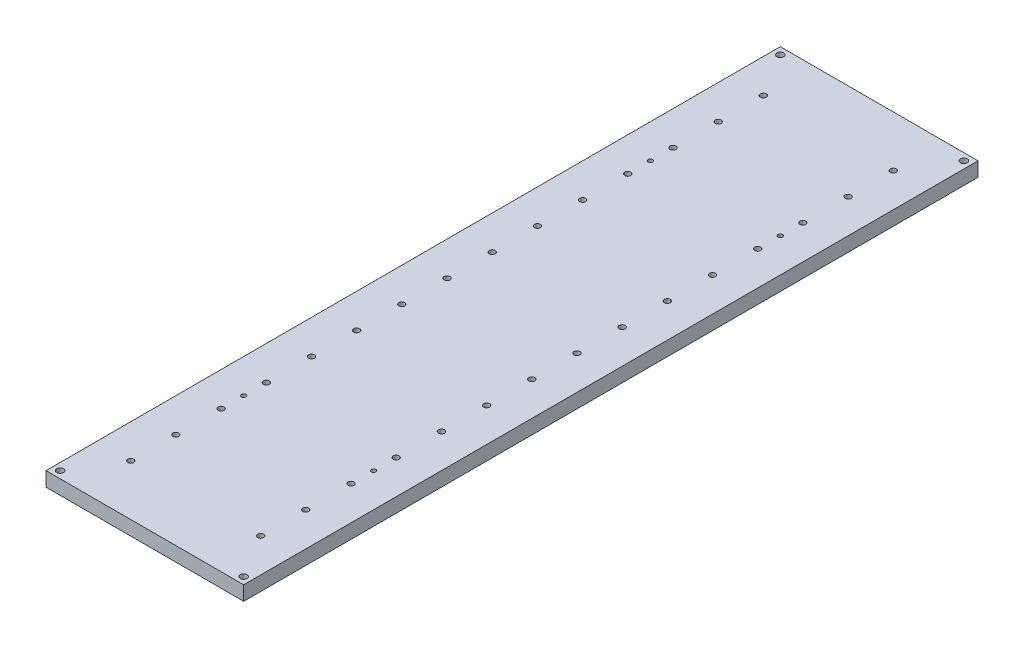
SolidWorks part; units mm, degrees
material "AISI 1020"
ref_plane "Plano frontal" through (0, 0, 0) normal (0, 0, 1) x (1, 0, 0)
ref_plane "Plano superior" through (0, 0, 0) normal (0, 1, 0) x (1, 0, 0)
ref_plane "Plano direito" through (0, 0, 0) normal (1, 0, 0) x (0, 0, -1)
sketch "Esboço1" plane through (0, 0, 0) normal (0, 0, 1) x (1, 0, 0)
  line L1 (-132, -12.7) -> (132, -12.7)
  line L2 (-132, -12.7) -> (-132, 12.7)
  line L3 (-132, 12.7) -> (132, 12.7)
  line L4 (132, -12.7) -> (132, 12.7)
  line L5 (-132, -12.7) -> (132, 12.7) construction
  line L6 (-132, 12.7) -> (132, -12.7) construction
  point P0 (0, 0)
  dimension "D1" = 25.4
  dimension "D2" = 264
extrude "Ressalto-extrusão1" add sketch "Esboço1" along normal mid plane 1180
sketch "Esboço3" plane through (132, 0, 0) normal (1, 0, 0) x (0, 0, -1)
  line L4 (-590, -12.7) -> (590, -12.7)
  line L5 (-590, 12.7) -> (-590, -12.7)
  line L6 (590, 12.7) -> (-590, 12.7)
  line L7 (590, -12.7) -> (590, 12.7)
  line L8 (-590, -12.7) -> (590, -12.7)
  line L9 (-590, 12.7) -> (-590, -12.7)
  line L10 (590, 12.7) -> (-590, 12.7)
  line L11 (590, -12.7) -> (590, 12.7)
  dimension "D1" = 0
sketch "Esboço4" plane through (-132, 0, 0) normal (-1, 0, 0) x (0, 0, 1)
  line L4 (-590, -12.7) -> (590, -12.7)
  line L5 (590, -12.7) -> (590, 12.7)
  line L6 (590, 12.7) -> (-590, 12.7)
  line L7 (-590, 12.7) -> (-590, -12.7)
  line L8 (-590, -12.7) -> (590, -12.7)
  line L9 (590, -12.7) -> (590, 12.7)
  line L10 (590, 12.7) -> (-590, 12.7)
  line L11 (-590, 12.7) -> (-590, -12.7)
  dimension "D1" = 0
extrude "Ressalto-extrusão3" add sketch "Esboço4" along normal blind 43
extrude "Ressalto-extrusão4" add sketch "Esboço3" along normal blind 43
hole_wizard "Rebaixo para parafuso Allen sextavado de M101" positions "Esboço6" profile "Esboço5" counterbore size "M10" standard "ISO" end condition through all
sketch "Esboço6" plane through (0, -12.7, 0) normal (0, -1, 0) x (-1, 0, 0)
  line L21 (175, 590) -> (175, -590) construction
  line L22 (-175, -590) -> (-175, 590) construction
  line L23 (-175, 590) -> (-175, -590) construction
  line L24 (175, -590) -> (175, 590) construction
  line L38 (-175, 590) -> (175, 590) construction
  point P4 (115, -320)
  point P10 (115, -240)
  point P84 (-115, 400)
  point P85 (-115, 240)
  point P86 (-115, 80)
  point P89 (-115, -80)
  point P90 (-115, -240)
  point P91 (-115, -400)
  point P154 (115, -480)
  point P155 (-115, -320)
  point P181 (-115, -160)
  point P186 (-115, 0)
  point P188 (-115, 160)
  point P196 (-115, 320)
  point P201 (-115, 480)
  point P202 (-115, 560)
  point P205 (115, 560)
  point P207 (-115, -480)
  point P210 (115, -400)
  point P215 (115, -80)
  point P217 (115, 0)
  point P219 (115, 80)
  point P221 (115, 160)
  point P223 (115, 320)
  point P225 (115, 240)
  point P227 (115, 400)
  point P229 (115, 480)
  point P234 (115, -160)
  point P240 (115, -560)
  point P244 (-115, -560)
  dimension "D2" = 60
  dimension "D3" = 80
  dimension "D5" = 80
  dimension "D6" = 80
  dimension "D7" = 80
  dimension "D8" = 80
  dimension "D9" = 80
  dimension "D10" = 80
  dimension "D11" = 60
  dimension "D12" = 60
  dimension "D13" = 60
  dimension "D14" = 60
  dimension "D15" = 60
  dimension "D16" = 60
  dimension "D17" = 60
  dimension "D18" = 80
  dimension "D19" = 80
  dimension "D20" = 80
  dimension "D21" = 80
  dimension "D22" = 80
  dimension "D23" = 80
  dimension "D24" = 80
  dimension "D25" = 80
  dimension "D26" = 80
  dimension "D27" = 80
  dimension "D28" = 80
  dimension "D29" = 30
  dimension "D30" = 80
  dimension "D31" = 80
  dimension "D32" = 80
  dimension "D33" = 80
  dimension "D34" = 80
  dimension "D35" = 80
  dimension "D36" = 80
  dimension "D37" = 80
  dimension "D38" = 80
  dimension "D39" = 80
  dimension "D40" = 80
  dimension "D41" = 30
  dimension "D42" = 60
  dimension "D43" = 60
  dimension "D44" = 60
  dimension "D45" = 60
  dimension "D46" = 60
  dimension "D47" = 60
  dimension "D48" = 60
  dimension "D49" = 60
  dimension "D50" = 60
  dimension "D51" = 60
  dimension "D52" = 60
  dimension "D53" = 60
  dimension "D54" = 60
  dimension "D55" = 60
  dimension "D56" = 60
  dimension "D57" = 60
sketch "Esboço5" plane through (-115, -12.7, 320) normal (1, 0, 0) x (0, 0, -1)
  line L0 (0, 0) -> (0, 25.4)
  line L1 (0, 25.4) -> (5.25, 25.4)
  line L3 (5.25, 25.4) -> (5.25, 10.6)
  line L4 (5.25, 10.6) -> (9, 10.6)
  line L5 (9, 10.6) -> (9, 0)
  line L7 (9, 0) -> (0, 0)
  line L11 (0, -6.35) -> (0, 107.95) construction
  dimension "Thru Hole Dia." = 10.5
  dimension "Thru Hole Depth" = 25.4
  dimension "C'Bore Dia." = 18
  dimension "C'Bore Depth" = 10.6
sketch "Esboço7" plane through (0, -12.7, 0) normal (0, -1, 0) x (1, 0, 0)
  line L0 (-175, 590) -> (-175, -590) construction
  line L1 (175, -590) -> (175, 590) construction
  circle A0 centre (-115, 360) radius 4
  circle A3 centre (115, 400) radius 5.25 construction
  circle A4 centre (115, 360) radius 4
  circle A5 centre (-115, 320) radius 5.25 construction
  point P6 (-88.8916, 480)
  point P7 (-88.8916, 480)
  dimension "D1" = 8
  dimension "D3" = 8
  dimension "D7" = 60
  dimension "D8" = 60
  dimension "D2" = 0
  dimension "D4" = 0
  dimension "D5" = 40
  dimension "D6" = 40
extrude "Corte-extrusão1" cut sketch "Esboço7" against normal through all
sketch "Esboço8" plane through (0, -12.7, 0) normal (0, -1, 0) x (1, 0, 0)
  line L0 (0, 652.0832) -> (0, 445.3456) construction
pattern_linear "Padrão linear1" count 2 spacing 720 along (0, 0, -1) of "Corte-extrusão1"
sketch "Esboço9" plane through (0, 0, 590) normal (0, 0, 1) x (1, 0, 0)
  line L4 (-175, -12.7) -> (175, -12.7)
  line L5 (175, -12.7) -> (175, 12.7)
  line L6 (175, 12.7) -> (-175, 12.7)
  line L7 (-175, 12.7) -> (-175, -12.7)
  line L8 (-175, -12.7) -> (175, -12.7)
  line L9 (175, -12.7) -> (175, 12.7)
  line L10 (175, 12.7) -> (-175, 12.7)
  line L11 (-175, 12.7) -> (-175, -12.7)
  dimension "D1" = 0
extrude "Ressalto-extrusão5" add sketch "Esboço9" along normal blind 60
sketch "Esboço10" plane through (0, 0, -590) normal (0, 0, -1) x (-1, 0, 0)
  line L4 (175, 12.7) -> (-175, 12.7)
  line L5 (-175, 12.7) -> (-175, -12.7)
  line L6 (-175, -12.7) -> (175, -12.7)
  line L7 (175, -12.7) -> (175, 12.7)
  line L8 (175, 12.7) -> (-175, 12.7)
  line L9 (-175, 12.7) -> (-175, -12.7)
  line L10 (-175, -12.7) -> (175, -12.7)
  line L11 (175, -12.7) -> (175, 12.7)
  dimension "D1" = 0
extrude "Ressalto-extrusão6" add sketch "Esboço10" along normal blind 60
sketch "Esboço12" plane through (0, 0, 650) normal (0, 0, 1) x (1, 0, 0)
  line L1 (-175, -12.7) -> (175, -12.7)
  line L2 (-175, -12.7) -> (-175, 12.7)
  line L3 (-175, 12.7) -> (175, 12.7)
  line L4 (175, -12.7) -> (175, 12.7)
  line L5 (-175, -12.7) -> (175, 12.7) construction
  line L6 (-175, 12.7) -> (175, -12.7) construction
  point P0 (0, 0)
extrude "Ressalto-extrusão7" [suppressed] add sketch "Esboço12" along normal blind 50
sketch "Esboço13" plane through (0, 0, -650) normal (0, 0, -1) x (-1, 0, 0)
  line L1 (175, -12.7) -> (-175, -12.7)
  line L2 (175, -12.7) -> (175, 12.7)
  line L3 (175, 12.7) -> (-175, 12.7)
  line L4 (-175, -12.7) -> (-175, 12.7)
  line L5 (175, -12.7) -> (-175, 12.7) construction
  line L6 (175, 12.7) -> (-175, -12.7) construction
  point P0 (0, 0)
extrude "Ressalto-extrusão8" [suppressed] add sketch "Esboço13" along normal blind 50
sketch "Esboço14" plane through (0, 0, 650) normal (0, 0, 1) x (1, 0, 0)
  line L1 (-175, -12.7) -> (175, -12.7)
  line L2 (-175, -12.7) -> (-175, 12.7)
  line L3 (-175, 12.7) -> (175, 12.7)
  line L4 (175, -12.7) -> (175, 12.7)
  line L5 (-175, -12.7) -> (175, 12.7) construction
  line L6 (-175, 12.7) -> (175, -12.7) construction
  point P0 (0, 0)
extrude "Ressalto-extrusão9" [suppressed] add sketch "Esboço14" along normal blind 50
sketch "Esboço15" plane through (0, 12.7, 0) normal (0, 1, 0) x (1, 0, 0)
  line L5 (-162.5, 637.5) -> (162.5, -637.5) construction
  line L6 (-162.5, -637.5) -> (162.5, 637.5) construction
  circle A0 centre (-162.5, -637.5) radius 3
  circle A1 centre (162.5, -637.5) radius 3
  circle A2 centre (-162.5, 637.5) radius 3
  circle A3 centre (162.5, 637.5) radius 3
  point P0 (0, 0)
  dimension "D3" = 6
  dimension "D4" = 6
  dimension "D5" = 6
  dimension "D6" = 6
  dimension "D7" = 325
  dimension "D1" = 1275
  dimension "D2" = 325
extrude "Corte-extrusão2" cut sketch "Esboço15" against normal through all
sketch "Esboço17" plane through (0, 12.7, 0) normal (0, 1, 0) x (1, 0, 0)
  line L1 (-150, -625) -> (-175, -625)
  line L2 (-150, -625) -> (-150, -650)
  line L3 (-150, -650) -> (-175, -650)
  line L4 (-175, -625) -> (-175, -650)
  line L5 (-150, -625) -> (-175, -650) construction
  line L6 (-150, -650) -> (-175, -625) construction
  line L7 (150, -625) -> (175, -625)
  line L8 (150, -625) -> (150, -650)
  line L9 (150, -650) -> (175, -650)
  line L10 (175, -625) -> (175, -650)
  line L11 (150, -625) -> (175, -650) construction
  line L12 (150, -650) -> (175, -625) construction
  line L13 (150, 625) -> (175, 625)
  line L14 (150, 625) -> (150, 650)
  line L15 (150, 650) -> (175, 650)
  line L16 (175, 625) -> (175, 650)
  line L17 (150, 625) -> (175, 650) construction
  line L18 (150, 650) -> (175, 625) construction
  line L19 (-150, 625) -> (-175, 625)
  line L20 (-150, 625) -> (-150, 650)
  line L21 (-150, 650) -> (-175, 650)
  line L22 (-175, 625) -> (-175, 650)
  line L23 (-150, 625) -> (-175, 650) construction
  line L24 (-150, 650) -> (-175, 625) construction
  point P0 (-162.5, -637.5)
  point P7 (162.5, -637.5)
  point P14 (162.5, 637.5)
  point P21 (-162.5, 637.5)
extrude "Corte-extrusão3" [suppressed] cut sketch "Esboço17" against normal blind 10
sketch "Esboço20" plane through (0, 12.7, 0) normal (0, 1, 0) x (1, 0, 0)
  circle A0 centre (-162.5, -637.5) radius 6
  circle A1 centre (162.5, -637.5) radius 6
  circle A2 centre (-162.5, 637.5) radius 6
  circle A3 centre (162.5, 637.5) radius 6
  dimension "D1" = 12
  dimension "D2" = 12
  dimension "D3" = 12
  dimension "D4" = 12
extrude "Corte-extrusão4" cut sketch "Esboço20" against normal blind 10
